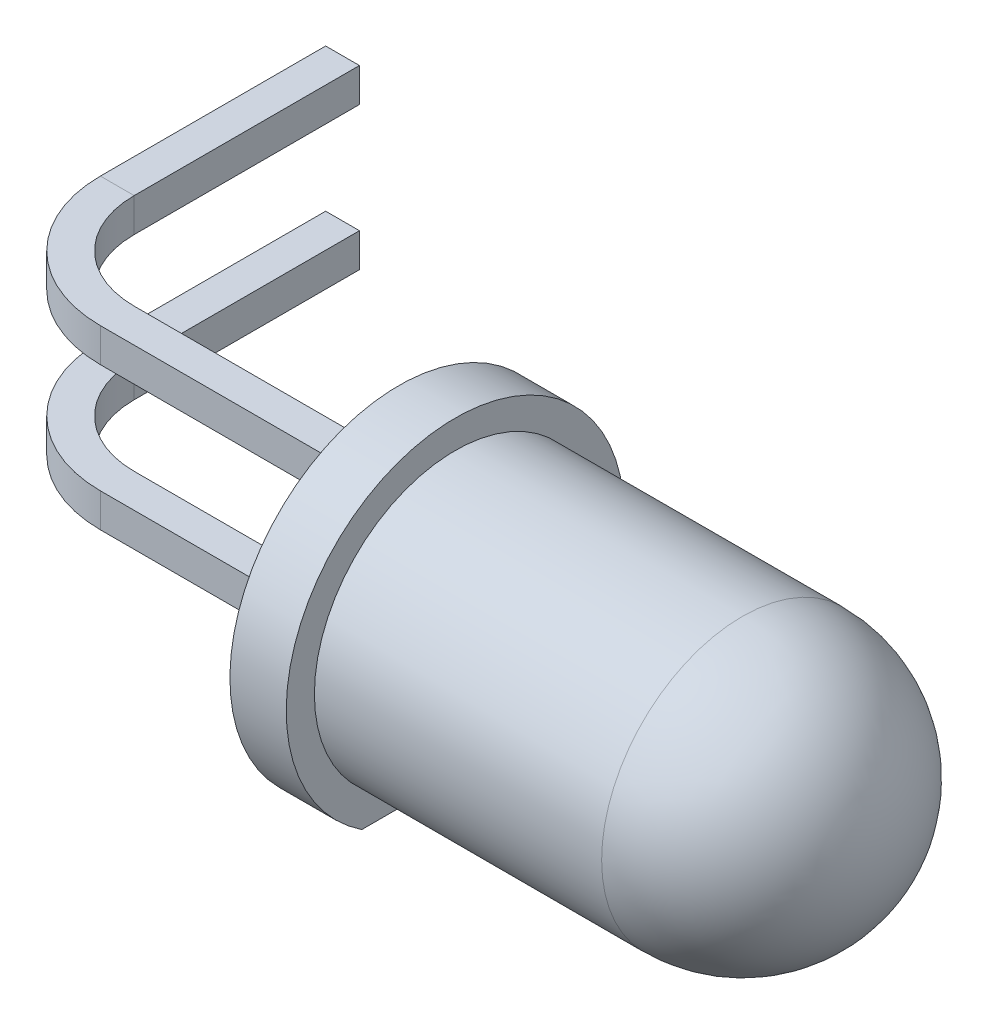
SolidWorks part; units mm, degrees
material "ABS PC"
ref_plane "Plan de face" through (0, 0, 0) normal (0, 0, 1) x (1, 0, 0)
ref_plane "Plan de dessus" through (0, 0, 0) normal (0, 1, 0) x (1, 0, 0)
ref_plane "Plan de droite" through (0, 0, 0) normal (1, 0, 0) x (0, 0, -1)
sketch "Esquisse1" plane through (0, 0, 0) normal (0, 0, 1) x (1, 0, 0)
  line L0 (-3.6521, 0) -> (13.862, 0) construction
  line L1 (0, 0) -> (0, 3)
  line L2 (0, 3) -> (1, 3)
  line L3 (1, 3) -> (1, 2.5)
  line L4 (1, 2.5) -> (6.1, 2.5)
  line L5 (6.1, 2.6056) -> (6.1, -2.7231) construction
  line L6 (0.05, 0) -> (0.05, 2.95)
  line L7 (0.05, 2.95) -> (0.95, 2.95)
  line L8 (0.95, 2.95) -> (0.95, 2.45)
  line L9 (0.95, 2.45) -> (6.1, 2.45)
  line L10 (0, 0) -> (0.05, 0)
  line L11 (8.55, 0) -> (8.6, 0)
  arc A0 (8.6, 0) -> (6.1, 2.5) centre (6.1, 0) ccw
  arc A1 (8.55, 0) -> (6.1, 2.45) centre (6.1, 0) ccw
  point P12 (1, 2.75)
  dimension "D4" = 5
  dimension "D1" = 6.1
  dimension "D2" = 1
  dimension "D3" = 3
  dimension "D5" = 0.05
revolve "Révolution1" add sketch "Esquisse1" angle 360 about L0
sketch "Esquisse2" plane through (0, 0, 0) normal (-1, 0, 0) x (0, 0, 1)
  line L0 (-3.5096, 0) -> (3.427, 0) construction
  line L1 (0, 3.2578) -> (0, -3.2845) construction
  line L2 (-2.3205, -2.5) -> (2.6012, -2.5)
  line L3 (2.6012, -2.5) -> (2.6012, -3.2845)
  line L4 (2.6012, -3.2845) -> (-2.3205, -3.2845)
  line L5 (-2.3205, -3.2845) -> (-2.3205, -2.5)
  dimension "D1" = 2.5
extrude "Enlèv. mat.-Extru.1" cut sketch "Esquisse2" against normal through all
sketch "Esquisse3" plane through (0, 0, 0) normal (-1, 0, 0) x (0, 0, 1)
  line L0 (-3.361, 0) -> (3.8833, 0) construction
  line L1 (-0.3, -0.97) -> (0.3, -0.97)
  line L2 (-0.3, -0.97) -> (-0.3, -1.57)
  line L3 (-0.3, -1.57) -> (0.3, -1.57)
  line L4 (0.3, -0.97) -> (0.3, -1.57)
  line L5 (0, -3.2654) -> (0, 3.7545) construction
  line L6 (-0.6104, -1.27) -> (0.5014, -1.27) construction
  line L7 (-0.3, 1.57) -> (0.3, 1.57)
  line L8 (0.3, 0.97) -> (0.3, 1.57)
  line L9 (-0.3, 0.97) -> (-0.3, 1.57)
  line L10 (-0.3, 0.97) -> (0.3, 0.97)
  dimension "D1" = 0.6
  dimension "D2" = 0.6
  dimension "D3" = 1.27
ref_plane "Plan1" through (0, -1.27, 0) normal (0, 1, 0) x (1, 0, 0)
sketch "Esquisse4" plane through (0, -1.27, 0) normal (0, 1, 0) x (1, 0, 0)
  line L0 (10.9708, 0) -> (-9.8378, 0) construction
  line L1 (-7.8053, 2) -> (-4.1408, 2) construction
  line L3 (-7, 2) -> (-7, 6)
  line L4 (-5, 2.6724) -> (-5, -0.6945) construction
  arc A1 (-5, 0) -> (-7, 2) centre (-5, 2) cw
  dimension "D3" = 2
  dimension "D1" = 6
  dimension "D2" = 5
  dimension "D5" = 2
extrude "Boss.-Extru.2" add sketch "Esquisse3" along normal blind 5 and the other way blind 5
sketch "Esquisse5" plane through (-5, 0, 0) normal (-1, 0, 0) x (0, 0, 1)
  line L0 (0.3, 0.97) -> (0.3, 1.57) construction
  line L1 (0.3, 1.57) -> (-0.3, 1.57) construction
  line L2 (-0.3, 1.57) -> (-0.3, 0.97) construction
  line L3 (0.3, 0.97) -> (-0.3, 0.97) construction
  line L4 (-0.3, -0.97) -> (-0.3, -1.57)
  line L5 (-0.3, -1.57) -> (0.3, -1.57)
  line L6 (0.3, -1.57) -> (0.3, -0.97)
  line L7 (0.3, -0.97) -> (-0.3, -0.97)
  line L8 (-0.3, -0.97) -> (-0.3, -1.57)
  line L9 (-0.3, -1.57) -> (0.3, -1.57)
  line L10 (0.3, -1.57) -> (0.3, -0.97)
  line L11 (0.3, -0.97) -> (-0.3, -0.97)
  line L12 (0.3, 0.97) -> (0.3, 1.57)
  line L13 (0.3, 1.57) -> (-0.3, 1.57)
  line L14 (-0.3, 1.57) -> (-0.3, 0.97)
  line L15 (0.3, 0.97) -> (-0.3, 0.97)
  dimension "D1" = 0
sketch "Esquisse6" plane through (0, 0, 0.3) normal (0, 0, 1) x (1, 0, 0)
  line L0 (5, 0.27) -> (5, -1.57)
  line L1 (4.5, 0.27) -> (3, -0.57)
  line L2 (3, -0.57) -> (3, -1.57)
  line L3 (5, 0.27) -> (4.5, 0.27)
  line L4 (3, -1.57) -> (5, -1.57)
  line L8 (0, 3) -> (0, -2.5) construction
  line L9 (-0.6821, 0) -> (5.6073, 0) construction
  point P1 (5, -2.0472)
  dimension "D1" = 5
  dimension "D2" = 2
  dimension "D3" = 0.27
  dimension "D5" = 1.57
  dimension "D4" = 0.5
  dimension "D6" = 1
extrude "Boss.-Extru.3" add sketch "Esquisse6" against normal blind 0.6
sketch "Esquisse7" plane through (0, 0, 0.3) normal (0, 0, 1) x (1, 0, 0)
  line L0 (4.5, 0.9747) -> (3, 0.1347)
  line L1 (3, 0.1347) -> (3, 0.9747)
  line L2 (3, 0.9747) -> (4.5, 0.9747)
  line L3 (-0.9845, 0) -> (6.7725, 0) construction
  line L5 (0, -4.0286) -> (0, 3.8768) construction
  dimension "D1" = 29.25
  dimension "D2" = 4.5
  dimension "D3" = 1.5
  dimension "D4" = 0.9747
extrude "Boss.-Extru.4" add sketch "Esquisse7" against normal blind 0.6
sweep "Balayage4" add profiles "Esquisse5" path "Esquisse4"
